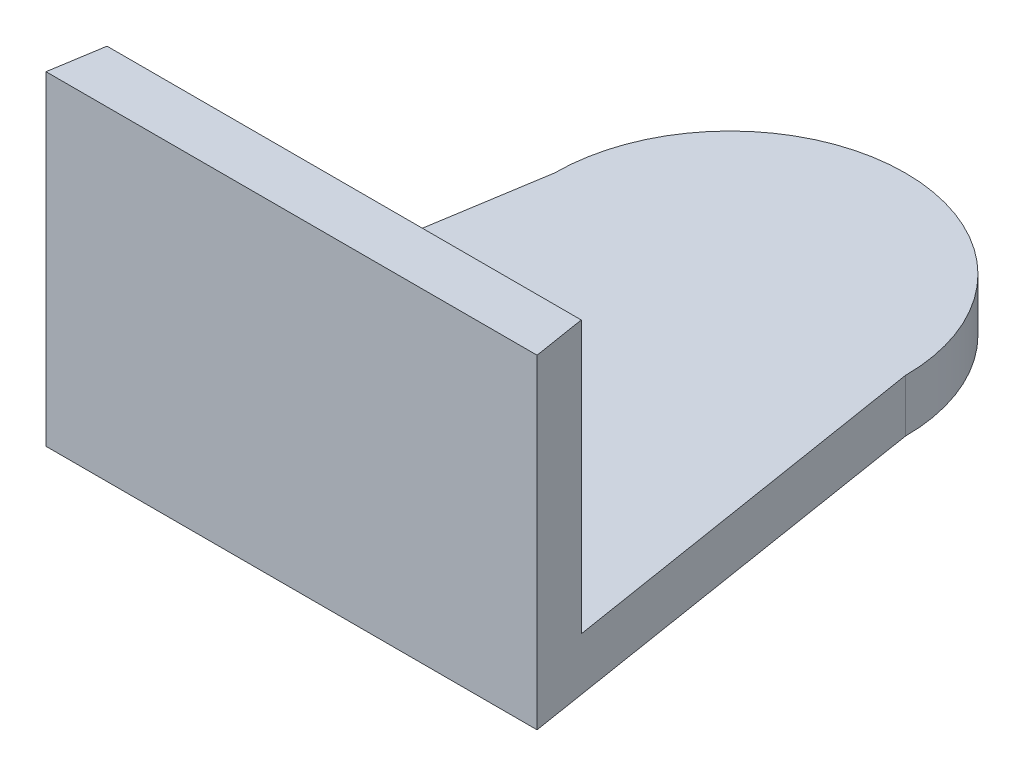
SolidWorks part; units mm, degrees
material "Custom Plastic"
ref_plane "Front Plane" through (0, 0, 0) normal (0, 0, 1) x (1, 0, 0)
ref_plane "Top Plane" through (0, 0, 0) normal (0, 1, 0) x (1, 0, 0)
ref_plane "Right Plane" through (0, 0, 0) normal (1, 0, 0) x (0, 0, -1)
sketch "Sketch1" plane through (0, 0, 0) normal (0, 1, 0) x (1, 0, 0)
  line L0 (-10, 0) -> (-14, -25)
  line L1 (10, 0) -> (14, -25)
  line L2 (0, 17.2103) -> (0, -39.4896) construction
  line L3 (-14, -25) -> (14, -25)
  arc A0 (-10, 0) -> (10, 0) centre (0, 0) cw
  dimension "D1" = 10
  dimension "D2" = 25
  dimension "D3" = 14
extrude "Boss-Extrude1" add sketch "Sketch1" along normal blind 3
sketch "Sketch5" plane through (0, 3, 0) normal (0, 1, 0) x (1, 0, 0)
  line L0 (-13.52, -22) -> (13.52, -22)
  line L1 (-10, 0) -> (-14, -25) construction
  line L2 (14, -25) -> (10, 0) construction
  line L3 (-13.52, -22) -> (-14, -25)
  line L4 (-14, -25) -> (14, -25)
  line L5 (14, -25) -> (13.52, -22)
  dimension "D1" = 3
extrude "Boss-Extrude2" add sketch "Sketch5" along normal blind 15.5
